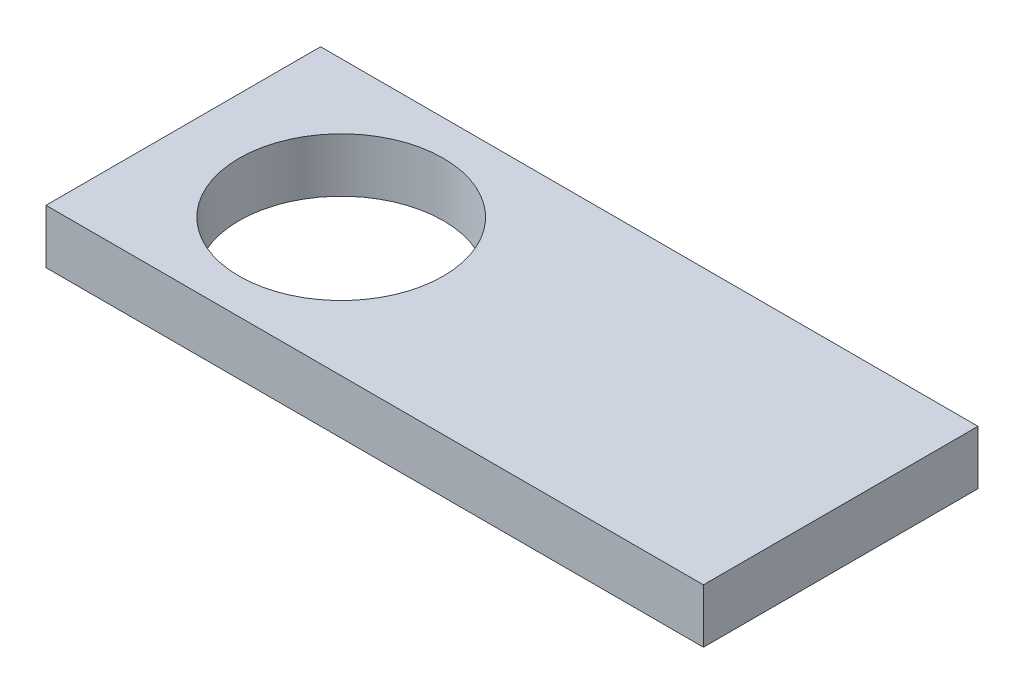
SolidWorks part; units mm, degrees
ref_plane "Front Plane" through (0, 0, 0) normal (0, 0, 1) x (1, 0, 0)
ref_plane "Top Plane" through (0, 0, 0) normal (0, 1, 0) x (1, 0, 0)
ref_plane "Right Plane" through (0, 0, 0) normal (1, 0, 0) x (0, 0, -1)
sketch "Sketch1" plane through (0, 0, 0) normal (0, 1, 0) x (1, 0, 0)
  line L0 (0, 0) -> (76.61, 0)
  line L1 (76.61, 0) -> (76.61, 32)
  line L3 (0, 32) -> (0, 0)
  line L4 (0, 32) -> (76.61, 32)
  circle A0 centre (18.4, 16) radius 11.9
extrude "Boss-Extrude2" add sketch "Sketch1" along normal blind 6.3 contours L0 L1 L4 L3
sketch "Sketch2" plane through (0, 6.3, 0) normal (0, 1, 0) x (1, 0, 0)
  circle A0 centre (18.4, 16) radius 11.9
extrude "Cut-Extrude1" cut sketch "Sketch2" against normal blind 6.3
